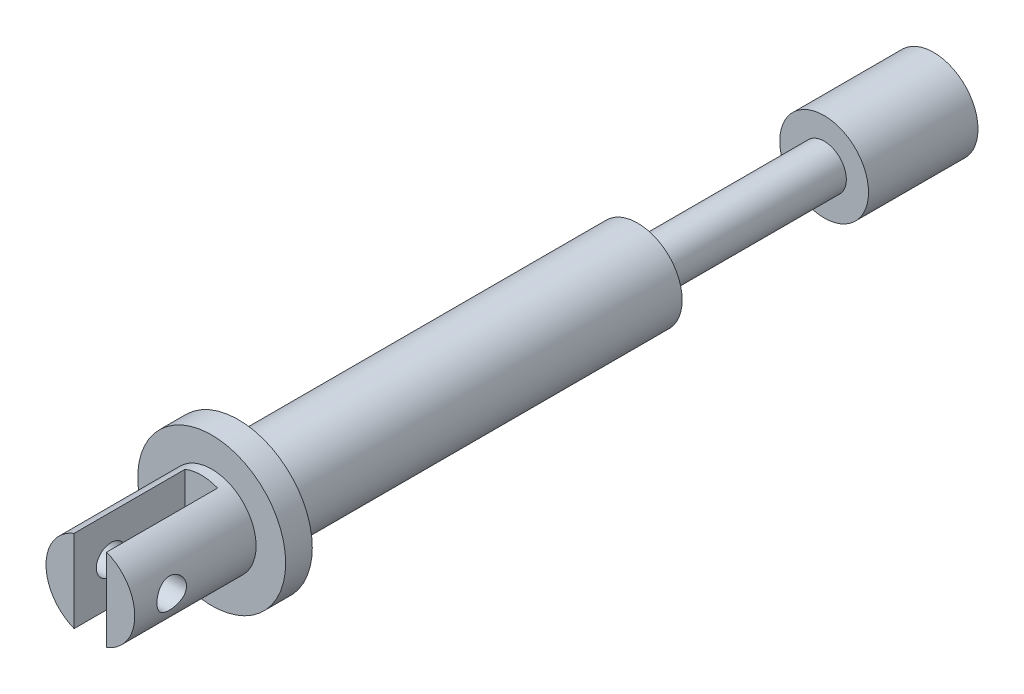
SolidWorks part; units mm, degrees
ref_plane "Front Plane" through (0, 0, 0) normal (0, 0, 1) x (1, 0, 0)
ref_plane "Top Plane" through (0, 0, 0) normal (0, 1, 0) x (1, 0, 0)
ref_plane "Right Plane" through (0, 0, 0) normal (1, 0, 0) x (0, 0, -1)
sketch "Sketch1" plane through (0, 0, 0) normal (0, 0, 1) x (1, 0, 0)
  circle A0 centre (0, 0) radius 1.5
  dimension "D1" = 3
extrude "Boss-Extrude1" add sketch "Sketch1" along normal mid plane 57
sketch "Sketch2" plane through (0, 0, 28.5) normal (0, 0, 1) x (1, 0, 0)
  circle A0 centre (0, 0) radius 3
  dimension "D1" = 6
extrude "Boss-Extrude2" add sketch "Sketch2" against normal blind 37
ref_plane "Plane1" through (0, 0, 18.5) normal (0, 0, 1) x (1, 0, 0)
ref_plane "Plane2" through (0, 0, -21.1) normal (0, 0, -1) x (-1, 0, 0)
sketch "Sketch5" plane through (0, 0, 18.5) normal (0, 0, 1) x (1, 0, 0)
  circle A0 centre (0, 0) radius 5
  dimension "D1" = 10
extrude "Boss-Extrude3" add sketch "Sketch5" along normal blind 1.8
sketch "Sketch6" plane through (0, 0, -21.1) normal (0, 0, -1) x (-1, 0, 0)
  circle A0 centre (0, 0) radius 3
  dimension "D1" = 6
extrude "Boss-Extrude4" add sketch "Sketch6" along normal up to surface (7.4 mm away) up to face at (1.5, 0, -28.5)
sketch "Sketch3" plane through (0, 0, 0) normal (0, 1, 0) x (1, 0, 0)
  line L0 (-1.1, -21) -> (1.1, -21)
  line L1 (-1.1, -21) -> (-1.1, -28.5)
  line L2 (1.1, -21) -> (1.1, -28.5)
  line L3 (-1.1, -28.5) -> (1.1, -28.5)
  line L4 (-3, -28.5) -> (3, -28.5) construction
  line L5 (0, -28.5) -> (0, -21) construction
  dimension "D1" = 2.2
  dimension "D2" = 7.5
extrude "Cut-Extrude1" cut sketch "Sketch3" against normal through all both and the other way through all
sketch "Sketch4" plane through (0, 0, 0) normal (1, 0, 0) x (0, 0, -1)
  line L0 (-26, 0) -> (0, 0) construction
  line L1 (-28.5, 2.7911) -> (-28.5, -2.7911) construction
  circle A0 centre (-26, 0) radius 1
  dimension "D2" = 2
  dimension "2.7" = 2.5
extrude "Cut-Extrude2" cut sketch "Sketch4" against normal through all both and the other way through all
